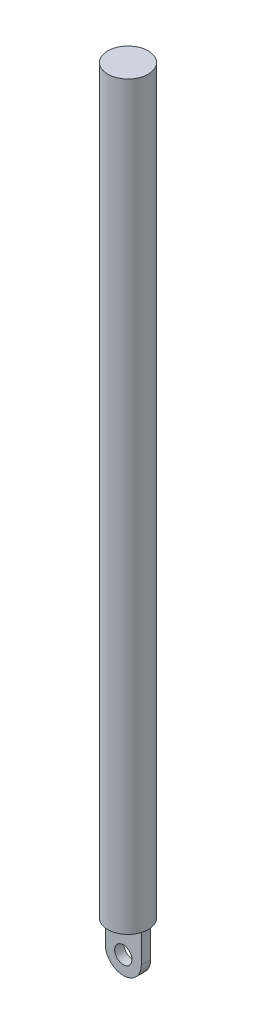
SolidWorks part; units mm, degrees
ref_plane "Front Plane" through (0, 0, 0) normal (0, 0, 1) x (1, 0, 0)
ref_plane "Top Plane" through (0, 0, 0) normal (0, 1, 0) x (1, 0, 0)
ref_plane "Right Plane" through (0, 0, 0) normal (1, 0, 0) x (0, 0, -1)
sketch "Sketch1" plane through (0, 0, 0) normal (0, 1, 0) x (1, 0, 0)
  circle A0 centre (0, 0) radius 3.395
  dimension "D1" = 6.79
extrude "Boss-Extrude1" add sketch "Sketch1" along normal blind 124.37
sketch "Sketch2" plane through (0, 0, 0) normal (0, 0, 1) x (1, 0, 0)
  line L1 (3.395, 0) -> (-3.395, 0) construction
  line L2 (3.025, 0) -> (-3.025, 0)
  point P8 (0, 0)
  dimension "D1" = 6.05
sketch "Sketch3" plane through (0, 0, 0) normal (0, 1, 0) x (1, 0, 0)
  line L0 (3.025, 0) -> (-3.025, 0) construction
  line L1 (3.025, 0) -> (-3.025, 0)
  line L3 (3.025, 0.785) -> (-3.025, 0.785)
  line L4 (3.025, 0.785) -> (3.025, -0.785)
  line L5 (3.025, -0.785) -> (-3.025, -0.785)
  line L6 (-3.025, 0.785) -> (-3.025, -0.785)
  line L7 (3.025, 0.785) -> (-3.025, -0.785) construction
  line L8 (3.025, -0.785) -> (-3.025, 0.785) construction
  point P2 (0, 0)
  dimension "D1" = 1.57
extrude "Boss-Extrude2" add sketch "Sketch3" against normal blind 7.98 contours L3 L6 L1 L4 | L1 L6 L5 L4
sketch "Sketch4" plane through (0, 0, -0.785) normal (0, 0, -1) x (-1, 0, 0)
  line L0 (0, 0) -> (0, -7.98) construction
  line L1 (-3.025, 0) -> (3.025, 0) construction
  line L2 (-3.025, -7.98) -> (3.025, -7.98) construction
  line L3 (3.025, -7.98) -> (3.025, 0) construction
  line L8 (-3.025, -4.955) -> (-5.5513, -4.955)
  line L9 (-5.5513, -4.955) -> (-3.3563, -8.8341)
  line L10 (-3.3563, -8.8341) -> (4.9872, -9.532)
  line L11 (4.9872, -9.532) -> (4.8862, -4.955)
  line L12 (4.8862, -4.955) -> (3.025, -4.955)
  arc A0 (-3.025, -4.955) -> (3.025, -4.955) centre (0, -4.955) ccw
extrude "Cut-Extrude1" cut sketch "Sketch4" against normal blind 7.98
sketch "Sketch5" plane through (0, 0, -0.785) normal (0, 0, -1) x (-1, 0, 0)
  circle A0 centre (0, -4.955) radius 1.45
  arc A1 (-3.025, -4.955) -> (3.025, -4.955) centre (0, -4.955) ccw construction
  dimension "D1" = 2.9
extrude "Cut-Extrude2" cut sketch "Sketch5" against normal blind 7.98
